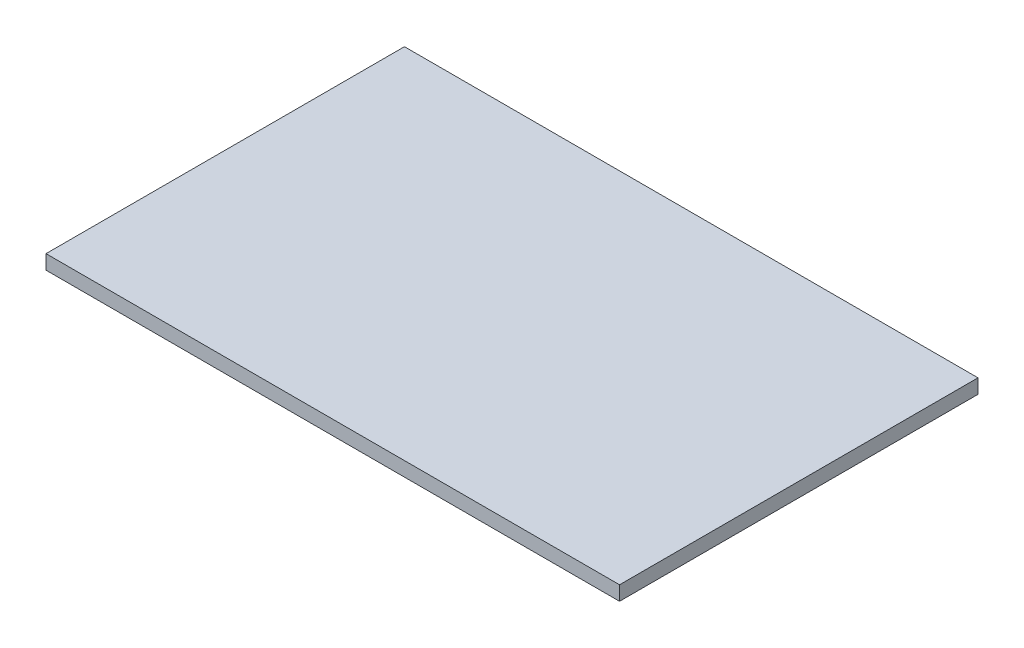
SolidWorks part; units mm, degrees
ref_plane "Front Plane" through (0, 0, 0) normal (0, 0, 1) x (1, 0, 0)
ref_plane "Top Plane" through (0, 0, 0) normal (0, 1, 0) x (1, 0, 0)
ref_plane "Right Plane" through (0, 0, 0) normal (1, 0, 0) x (0, 0, -1)
sketch "Sketch1" plane through (0, 0, 0) normal (0, 1, 0) x (1, 0, 0)
  line L1 (-45.8351, 21.491) -> (34.1649, 21.491)
  line L2 (-45.8351, 21.491) -> (-45.8351, -28.509)
  line L3 (-45.8351, -28.509) -> (34.1649, -28.509)
  line L4 (34.1649, 21.491) -> (34.1649, -28.509)
  dimension "D1" = 50
  dimension "D2" = 80
extrude "Boss-Extrude1" add sketch "Sketch1" along normal blind 2
